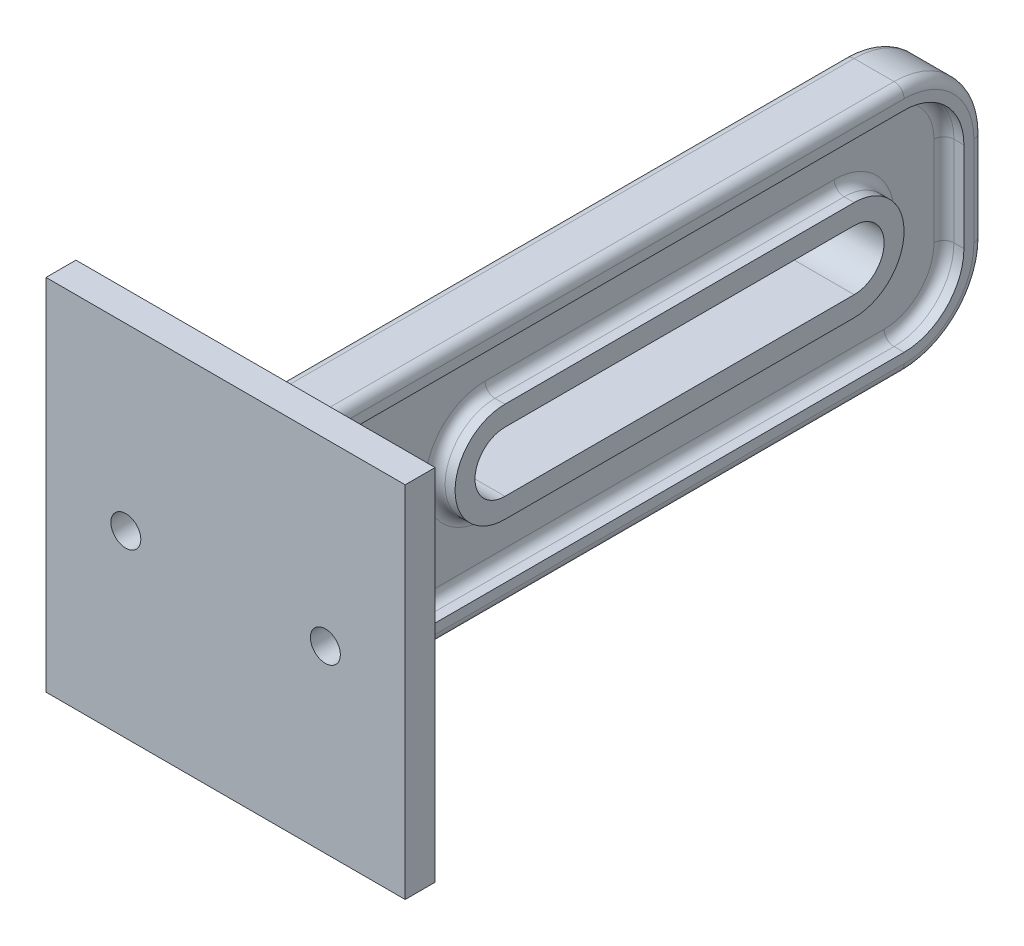
SolidWorks part; units mm, degrees
ref_plane "Front Plane" through (0, 0, 0) normal (0, 0, 1) x (1, 0, 0)
ref_plane "Top Plane" through (0, 0, 0) normal (0, 1, 0) x (1, 0, 0)
ref_plane "Right Plane" through (0, 0, 0) normal (1, 0, 0) x (0, 0, -1)
sketch "Sketch2" plane through (0, 0, 0) normal (0, 0, 1) x (1, 0, 0)
  line L1 (18, -18) -> (-18, -18)
  line L2 (18, -18) -> (18, 18)
  line L3 (18, 18) -> (-18, 18)
  line L4 (-18, -18) -> (-18, 18)
  line L5 (18, -18) -> (-18, 18) construction
  line L6 (18, 18) -> (-18, -18) construction
  point P0 (0, 0)
  dimension "D1" = 36
  dimension "D2" = 36
extrude "Boss-Extrude1" add sketch "Sketch2" along normal blind 3
sketch "Sketch3" plane through (0, 0, 0) normal (0, 0, -1) x (-1, 0, 0)
  line L0 (0, 0) -> (0, -20.721) construction
  circle A0 centre (10, 0) radius 1.5
  circle A1 centre (-10, 0) radius 1.5
  point P7 (10, 0)
  dimension "D1" = 3
  dimension "D2" = 3
  dimension "D3" = 20
extrude "Cut-Extrude1" cut sketch "Sketch3" against normal blind 3
sketch "Sketch4" plane through (0, 0, 0) normal (0, 0, -1) x (-1, 0, 0)
  line L1 (-3, -12.5) -> (3, -12.5)
  line L2 (-3, -12.5) -> (-3, 12.5)
  line L3 (-3, 12.5) -> (3, 12.5)
  line L4 (3, -12.5) -> (3, 12.5)
  line L5 (-3, -12.5) -> (3, 12.5) construction
  line L6 (-3, 12.5) -> (3, -12.5) construction
  point P0 (0, 0)
  dimension "D1" = 25
  dimension "D2" = 6
extrude "Boss-Extrude2" add sketch "Sketch4" along normal blind 70
sketch "Sketch5" plane through (3, 0, 0) normal (1, 0, 0) x (0, 0, -1)
  line L0 (57, 0) -> (22, 0) construction
  line L1 (57, -3) -> (22, -3)
  line L2 (57, 3) -> (22, 3)
  line L4 (70, 12.5) -> (70, -12.5) construction
  arc A0 (57, -3) -> (57, 3) centre (57, 0) ccw
  arc A1 (22, 3) -> (22, -3) centre (22, 0) ccw
  point P3 (39.5, 0)
  point P8 (42.2777, 0)
  point P9 (60, 0)
  dimension "D1" = 3
  dimension "D2" = 10
  dimension "D3" = 35
extrude "Cut-Extrude2" cut sketch "Sketch5" against normal blind 70
fillet "Fillet1" radius 8 2 edges at (0, 12.5, -70) (0, -12.5, -70)
sketch "Sketch7" plane through (3, 0, 0) normal (1, 0, 0) x (0, 0, -1)
  line L8 (68, -4.5) -> (68, 4.5)
  line L9 (62, 10.5) -> (2, 10.5)
  line L10 (2, 10.5) -> (2, -10.5)
  line L11 (2, -10.5) -> (62, -10.5)
  line L12 (68, -4.5) -> (68, 4.5)
  line L13 (62, 10.5) -> (2, 10.5)
  line L14 (2, 10.5) -> (2, -10.5)
  line L15 (2, -10.5) -> (62, -10.5)
  line L23 (57, 5) -> (22, 5)
  line L24 (22, -5) -> (57, -5)
  line L25 (57, 5) -> (22, 5)
  line L26 (22, -5) -> (57, -5)
  arc A4 (68, 4.5) -> (62, 10.5) centre (62, 4.5) ccw
  arc A5 (62, -10.5) -> (68, -4.5) centre (62, -4.5) ccw
  arc A6 (68, 4.5) -> (62, 10.5) centre (62, 4.5) ccw
  arc A7 (62, -10.5) -> (68, -4.5) centre (62, -4.5) ccw
  arc A18 (22, 5) -> (22, -5) centre (22, 0) ccw
  arc A19 (57, -5) -> (57, 5) centre (57, 0) ccw
  arc A20 (22, 5) -> (22, -5) centre (22, 0) ccw
  arc A21 (57, -5) -> (57, 5) centre (57, 0) ccw
  dimension "D1" = 2
  dimension "D2" = 2
extrude "Cut-Extrude3" cut sketch "Sketch7" against normal blind 2
mirror "Mirror1" about plane through (0, 0, 0) normal (1, 0, 0) of "Cut-Extrude3"
fillet "Fillet2" radius 1 10 edges at (-3, -12.5, -31) (-3, -10.1569, -67.6569) (-3, 12.5, -31) (-3, 10.1569, -67.6569) (3, 12.5, -31) (3, 10.1569, -67.6569) (3, -12.5, -31) (3, -10.1569, -67.6569) (-3, 0, -70) (3, 0, -70)
fillet "Fillet3" radius 1 10 edges at (-1, -10.5, -32) (-1, -8.7426, -66.2426) (-1, 10.5, -32) (-1, 8.7426, -66.2426) (1, -10.5, -32) (1, -8.7426, -66.2426) (1, 10.5, -32) (1, 8.7426, -66.2426) (-1, 0, -68) (1, 0, -68)
fillet "Fillet4" radius 1 8 edges at (-1, -5, -39.5) (-1, 0, -17) (-1, 5, -39.5) (1, -5, -39.5) (1, 0, -17) (1, 5, -39.5) (-1, 0, -62) (1, 0, -62)
fillet "Fillet5" radius 1 10 edges at (-2.5, 10.5, -2) (-1.2929, 10.2071, -2) (-2.5, -10.5, -2) (-1.2929, -10.2071, -2) (2.5, 10.5, -2) (1.2929, 10.2071, -2) (2.5, -10.5, -2) (1.2929, -10.2071, -2) (-1, 0, -2) (1, 0, -2)
fillet "Fillet6" radius 1 8 edges at (2.7071, 12.2071, 0) (0, 12.5, 0) (-2.7071, 12.2071, 0) (-3, 0, 0) (-2.7071, -12.2071, 0) (0, -12.5, 0) (2.7071, -12.2071, 0) (3, 0, 0)
